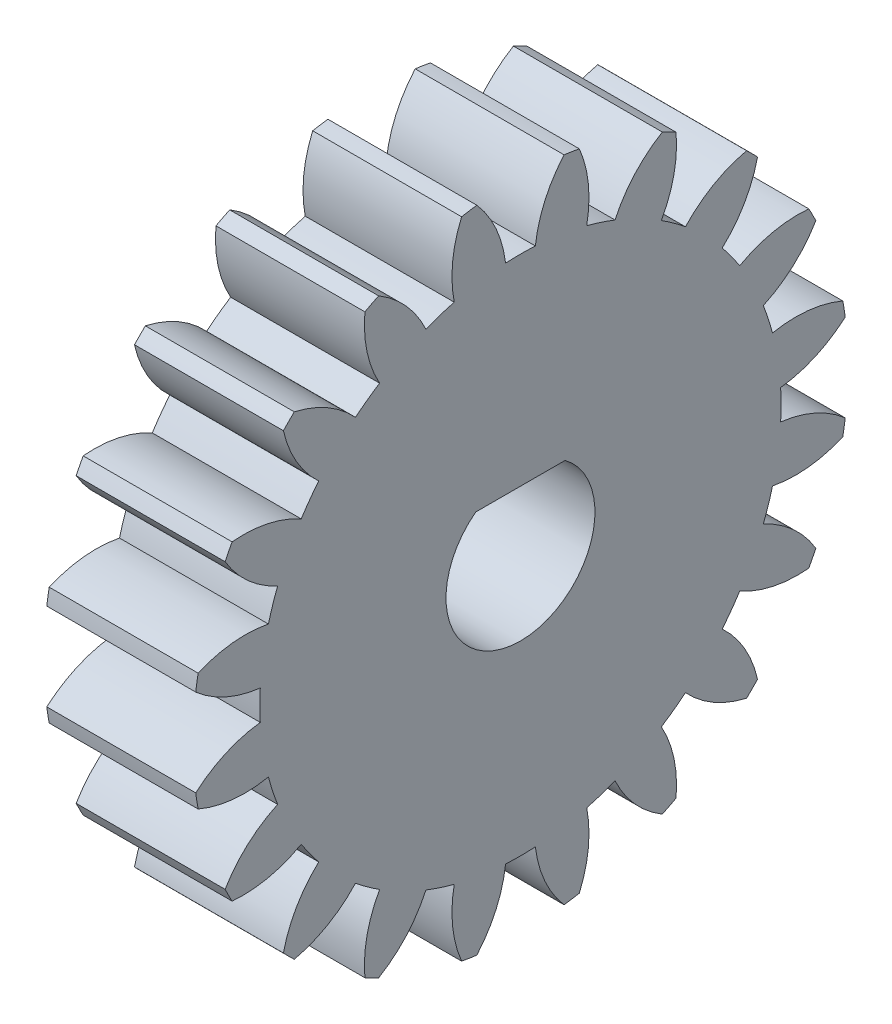
SolidWorks part; units mm, degrees
ref_plane "Plane1" through (0, 0, 0) normal (0, 0, 1) x (1, 0, 0)
ref_plane "Plane2" through (0, 0, 0) normal (0, 1, 0) x (1, 0, 0)
ref_plane "Plane3" through (0, 0, 0) normal (1, 0, 0) x (0, 0, -1)
other "Configuration Table"
sketch "HoldingSke" plane through (0, 0, 0) normal (0, 1, 0) x (1, 0, 0)
  line L0 (0, 0) -> (0.9397, -0.342)
  line L1 (-15, 0) -> (100, 0) construction
  line L2 (0, 0) -> (-2.1039, 2.3779)
  line L3 (0, 0) -> (-11.863, 4.5341)
  line L4 (0, 0) -> (8.1152, 2.9537)
  line L5 (0, 0) -> (-46.8476, -17.4728)
  line L6 (0, 0) -> (-4.1448, -2.7965)
  line L7 (-2.1039, 2.3779) -> (8.6586, 51.2059)
  line L8 (-76.2, 54.61) -> (-75.7, 54.61)
  line L9 (-71.009, 38.7566) -> (-53.1078, 45.2721)
  line L10 (-76.2, 71.12) -> (104.1128, 71.12)
  line L11 (0, 0) -> (-5, 0)
  line L12 (-76.2, 101.6) -> (-76.162, 101.6)
  line L13 (24.9733, 27.94) -> (52.9518, 28.4284)
  line L14 (24.9733, 27.94) -> (24.9743, 27.94)
  line L15 (24.9733, 27.94) -> (100.4006, 29.5858)
  line L16 (-63.627, -1) -> (-12.827, -1)
  circle A0 centre (0, 0) radius 1.5
  circle A1 centre (0, 0) radius 8.749
  circle A2 centre (0, 0) radius 37.5
  circle A3 centre (0, 0) radius 1.5
  dimension "MHD" = 17.498
  dimension "Hub_dia" = 75
  dimension "Bore" = 3
  dimension "MBD" = 3
  dimension "Num_teeth" = 20
  dimension "Pitch" = 1
  dimension "Overall_len" = 50
  dimension "Show_teeth" = 20
  dimension "Thickness" = 5
  dimension "OAL" = 50.0001
  dimension "T_dim" = 0.5
  dimension "Ap" = 20
  dimension "H" = 19.05
  dimension "Pitch_radius" = 180.3128
  dimension "Width" = 5
  dimension "Backlash" = 0.038
  dimension "Addendum_fac" = 1
  dimension "Dedendum_fac" = 1.25
  dimension "Clearance_fac" = 0.25
  dimension "Dedendum_add" = 0.001
  dimension "Module" = 1
sketch "BasProSke" plane through (0, 0, 0) normal (0, 1, 0) x (1, 0, 0)
  line L0 (-10, 0) -> (60, 0) construction
  line L1 (0, 0) -> (0, 11)
  line L2 (0, 0) -> (5, 0)
  line L3 (5, 0) -> (5, 11)
  line L4 (5, 11) -> (0, 11)
  dimension "Thickness" = 5
  dimension "Diameter" = 22
revolve "Base-Revolve" add sketch "BasProSke" angle 360 about L0
sketch "TooCutSke" plane through (0, 0, 0) normal (1, 0, 0) x (0, 0, -1)
  line L1 (0, 0) -> (0, 107) construction
  line L2 (0, 0) -> (-0.8511, 9.9637) construction
  line L3 (0, 0) -> (-3.1206, 19.7028) construction
  line L4 (-0.8511, 9.9637) -> (-1.5603, 9.8514) construction
  arc A0 (0.4999, 8.7347) -> (-0.4999, 8.7347) centre (0, 0) ccw
  arc A1 (1.4852, 10.9249) -> (-1.4852, 10.9249) centre (0, 0) ccw
  circle A2 centre (0, 0) radius 10 construction
  circle A3 centre (0, 0) radius 9.3969 construction
  arc A4 (-0.4999, 8.7347) -> (-1.4852, 10.9249) centre (-4.4722, 8.2645) ccw
  arc A5 (1.4852, 10.9249) -> (0.4999, 8.7347) centre (4.4722, 8.2645) ccw
  dimension "Root_dia" = 17.498
  dimension "Overcut_dia" = 22.0508
  dimension "Pitch_dia" = 20
  dimension "Base_dia" = 18.7939
  dimension "Flank_rad" = 4
  dimension "Half_ang" = 9
  dimension "Half_CT" = 0.7181
extrude "ToothCut" cut sketch "TooCutSke" along normal through all
fillet "Breaks" [suppressed] radius 0.02
fillet "RootFillets" [suppressed] radius 0.251
pattern_circular "TeethCuts" count 20 every 18 about axis through (-10, 0, 0) along (1, 0, 0) of "ToothCut", "RootFillets", "Breaks"
sketch "HubNeaOneSke" plane through (0, 0, 0) normal (-1, 0, 0) x (0, 0, 1)
  circle A0 centre (0, 0) radius 8.749
  dimension "Diameter" = 17.498
extrude "HubNearOne" [suppressed] add sketch "HubNeaOneSke" along normal blind 45.0001
sketch "HubNeaBotSke" plane through (0, 0, 0) normal (-1, 0, 0) x (0, 0, 1)
  circle A0 centre (0, 0) radius 8.749
  dimension "Diameter" = 17.498
extrude "HubNearBoth" [suppressed] add sketch "HubNeaBotSke" along normal blind 22.5
ref_plane "FarPln" through (5, 0, 0) normal (1, 0, 0) x (0, 0, -1)
sketch "HubFarSke" plane through (5, 0, 0) normal (1, 0, 0) x (0, 0, -1)
  circle A0 centre (0, 0) radius 8.749
  dimension "Diameter" = 17.498
extrude "HubFar" [suppressed] add sketch "HubFarSke" along normal blind 22.5
sketch "BorSke" plane through (0, 0, 0) normal (1, 0, 0) x (0, 0, -1)
  circle A0 centre (0, 0) radius 1.5
  dimension "Diameter" = 3
extrude "Bore" cut sketch "BorSke" along normal mid plane 100.0001
sketch "KeySke" plane through (0, 0, 0) normal (1, 0, 0) x (0, 0, -1)
  line L0 (-0.6, 0) -> (-0.6, 2)
  line L1 (-0.6, 2) -> (0.6, 2)
  line L2 (0.6, 2) -> (0.6, 0)
  line L3 (0, 0) -> (0, 34) construction
  line L4 (-0.6, 0) -> (0.6, 0)
  dimension "Offset" = 2
  dimension "Width" = 1.2
extrude "Keyway" [suppressed] cut sketch "KeySke" along normal mid plane 100.0001
pattern_circular "Keyway2" [suppressed] count 2 every 90 about axis through (-10, 0, 0) along (1, 0, 0)
sketch "Sketch1" plane through (5, 0, 0) normal (1, 0, 0) x (0, 0, -1)
  circle A0 centre (0, 0) radius 2.5
  dimension "D1" = 5
extrude "Cut-Extrude1" cut sketch "Sketch1" against normal blind 10
sketch "Sketch2" plane through (5, 0, 0) normal (1, 0, 0) x (0, 0, -1)
  line L0 (0, -2.5) -> (0, 1.5) construction
  line L2 (-3.1379, 1.5) -> (2.7704, 1.5)
  line L3 (-3.1379, 1.5) -> (-3.1379, 2.8976)
  line L4 (-3.1379, 2.8976) -> (2.7704, 2.8976)
  line L5 (2.7704, 1.5) -> (2.7704, 2.8976)
  circle A0 centre (0, 0) radius 2.5 construction
  dimension "D1" = 4
extrude "Boss-Extrude1" add sketch "Sketch2" against normal blind 5
sketch "Sketch3" plane through (0, 0, 0) normal (-1, 0, 0) x (0, 0, 1)
  circle A0 centre (0, 0) radius 2.5
extrude "Cut-Extrude2" cut sketch "Sketch3" against normal blind 10
sketch "Sketch4" plane through (0, 0, 0) normal (-1, 0, 0) x (0, 0, 1)
  line L0 (0, -2.5) -> (0, 2) construction
  line L2 (-2.3097, 2) -> (3.4349, 2)
  line L3 (-2.3097, 2) -> (-2.3097, 2.9167)
  line L4 (-2.3097, 2.9167) -> (3.4349, 2.9167)
  line L5 (3.4349, 2) -> (3.4349, 2.9167)
  circle A0 centre (0, 0) radius 2.5 construction
  dimension "D1" = 4.5
extrude "Boss-Extrude2" add sketch "Sketch4" against normal through all
equation "' \"Module@HoldingSke\" = 6.35"
equation "' \"Num_teeth@HoldingSke\" = 12"
equation "' \"Ap@HoldingSke\" =  20"
equation "' \"Ap@HoldingSke\" = 20"
equation "' \"Width@HoldingSke\" = 0.5 * 25.4"
equation "' \"Hub_dia@HoldingSke\"= 1 * 25.4"
equation "' \"Hub_dia@HoldingSke\" = 1 * 25.4"
equation "' \"Overall_len@HoldingSke\" = 1.0 * 25.4"
equation "' \"Bore@HoldingSke\" = 0.75 * 25.4"
equation "' \"T_dim@HoldingSke\" = 0.1 * 25.4"
equation "' \"Width@KeySke\" = 0.25 * 25.4"
equation "' \"Show_teeth@HoldingSke\" = 13"
equation "' \"Backlash@HoldingSke\" = 0.009 * 25.4"
equation "' \"Addendum_fac@HoldingSke\" = 1.0"
equation "' \"Dedendum_fac@HoldingSke\" = 1.25"
equation "' \"Dedendum_add@HoldingSke\" = 0.00005 * 25.4"
equation "' \"Clearance_fac@HoldingSke\" = 0.25"
equation "\"Pitch@HoldingSke\" = 1 / \"Module@HoldingSke\""
equation "\"Overcut_dia@TooCutSke\" = (\"Num_teeth@HoldingSke\" + 2 * \"Addendum_fac@HoldingSke\") / \"Pitch@HoldingSke\" + 0.002 * 25.4"
equation "\"Pitch_dia@TooCutSke\" = \"Num_teeth@HoldingSke\" / \"Pitch@HoldingSke\""
equation "\"Base_dia@TooCutSke\" = \"Num_teeth@HoldingSke\" / \"Pitch@HoldingSke\" * cos((\"Ap@HoldingSke\"  * 3.14159265 / 180))"
equation "\"Root_dia@TooCutSke\" = (\"Num_teeth@HoldingSke\" + 2) / \"Pitch@HoldingSke\" - 2 * (\"Addendum_fac@HoldingSke\" + \"Dedendum_fac@HoldingSke\") / \"Pitch@HoldingSke\" - \"Dedendum_add@HoldingSke\" * 2"
equation "\"Half_ang@TooCutSke\" = 180 / \"Num_teeth@HoldingSke\""
equation "\"Half_CT@TooCutSke\" = \"Num_teeth@HoldingSke\" / \"Pitch@HoldingSke\" * sin((3.14159265 / 2 / \"Num_teeth@HoldingSke\")) / 2 - 7 * \"Backlash@HoldingSke\" / 4"
equation "\"Flank_rad@TooCutSke\" = \"Num_teeth@HoldingSke\" / \"Pitch@HoldingSke\" / 5"
equation "\"Radius@RootFillets\" = \"Clearance_fac@HoldingSke\" / \"Pitch@HoldingSke\" + \"Dedendum_add@HoldingSke\""
equation "\"Break_rad@Breaks\" = 0.02 / \"Pitch@HoldingSke\""
equation "\"Thickness@HoldingSke\" = \"Width@HoldingSke\""
equation "\"OAL@HoldingSke\" = \"Thickness@HoldingSke\""
equation "\"MHD@HoldingSke\" = (\"Num_teeth@HoldingSke\" + 2) / \"Pitch@HoldingSke\" - 2 * (\"Addendum_fac@HoldingSke\" + \"Dedendum_fac@HoldingSke\")  / \"Pitch@HoldingSke\" - \"Dedendum_add@HoldingSke\" * 2"
equation "\"MBD@HoldingSke\" = (\"Num_teeth@HoldingSke\" + 2) / \"Pitch@HoldingSke\" - 2 * (\"Addendum_fac@HoldingSke\" + \"Dedendum_fac@HoldingSke\")  / \"Pitch@HoldingSke\" - \"Dedendum_add@HoldingSke\" * 2 - 0.002 * 25.4"
equation "\"MHD@HoldingSke\" = ((sgn( \"MHD@HoldingSke\" - \"Hub_dia@HoldingSke\" )-1)*( \"MHD@HoldingSke\" - \"Hub_dia@HoldingSke\" ))/-2+ \"Hub_dia@HoldingSke\""
equation "\"MBD@HoldingSke\" = ((sgn( \"MBD@HoldingSke\" - \"Bore@HoldingSke\" )-1)*( \"MBD@HoldingSke\" - \"Bore@HoldingSke\" ))/-2+ \"Bore@HoldingSke\""
equation "\"OAL@HoldingSke\" = ((sgn( \"OAL@HoldingSke\" - \"Overall_len@HoldingSke\" )+1)*( \"OAL@HoldingSke\" - \"Overall_len@HoldingSke\" ))/2 + \"Overall_len@HoldingSke\" + 0.000002 * 25.4"
equation "\"Num_teeth@TeethCuts\" = int( \"Show_teeth@HoldingSke\" ) + 1"
equation "\"Num_teeth@TeethCuts\" = ((sgn( \"Num_teeth@TeethCuts\" - \"Num_teeth@HoldingSke\" )-1)*( \"Num_teeth@TeethCuts\" - \"Num_teeth@HoldingSke\" ))/-2+ \"Num_teeth@HoldingSke\""
equation "\"Num_teeth@TeethCuts\" = ((sgn( \"Num_teeth@TeethCuts\" - 2.0)+1)*( \"Num_teeth@TeethCuts\" - 2.0))/2 +2.0"
equation "\"Angle@TeethCuts\" = 360.0 / \"Num_teeth@HoldingSke\""
equation "\"Diameter@BasProSke\" = (\"Num_teeth@HoldingSke\" + 2 * \"Addendum_fac@HoldingSke\") / \"Pitch@HoldingSke\""
equation "\"Thickness@BasProSke\"  = \"Thickness@HoldingSke\""
equation "' \"Fillet_rad@BasProSke\" =  \"Thickness@HoldingSke\" * 0.05"
equation "' \"Fillet_rad@BasProSke\" = \"Thickness@HoldingSke\" * 0.05"
equation "\"MHD@HoldingSke\" = ((sgn( \"MHD@HoldingSke\" - \"Root_dia@TooCutSke\" )-1)*( \"MHD@HoldingSke\" - \"Root_dia@TooCutSke\" ))/-2+ \"Root_dia@TooCutSke\""
equation "\"Diameter@HubNeaOneSke\" = \"MHD@HoldingSke\""
equation "\"Length@HubNearOne\" = \"OAL@HoldingSke\" - \"Thickness@BasProSke\""
equation "\"Diameter@HubNeaBotSke\" = \"MHD@HoldingSke\""
equation "\"Length@HubNearBoth\" = ( \"OAL@HoldingSke\" - \"Thickness@BasProSke\" ) / 2.0"
equation "\"Thickness@FarPln\" = \"Thickness@BasProSke\""
equation "\"Diameter@HubFarSke\" = \"MHD@HoldingSke\""
equation "\"Length@HubFar\" = ( \"OAL@HoldingSke\" - \"Thickness@BasProSke\" ) / 2.0"
equation "\"Diameter@BorSke\" = \"MBD@HoldingSke\""
equation "\"D1@Bore\" = \"OAL@HoldingSke\" * 2.0"
equation "\"D1@Keyway\" = \"OAL@HoldingSke\" * 2.0"
equation "\"Offset@KeySke\" = \"T_dim@HoldingSke\" + \"MBD@HoldingSke\" / 2.0"
